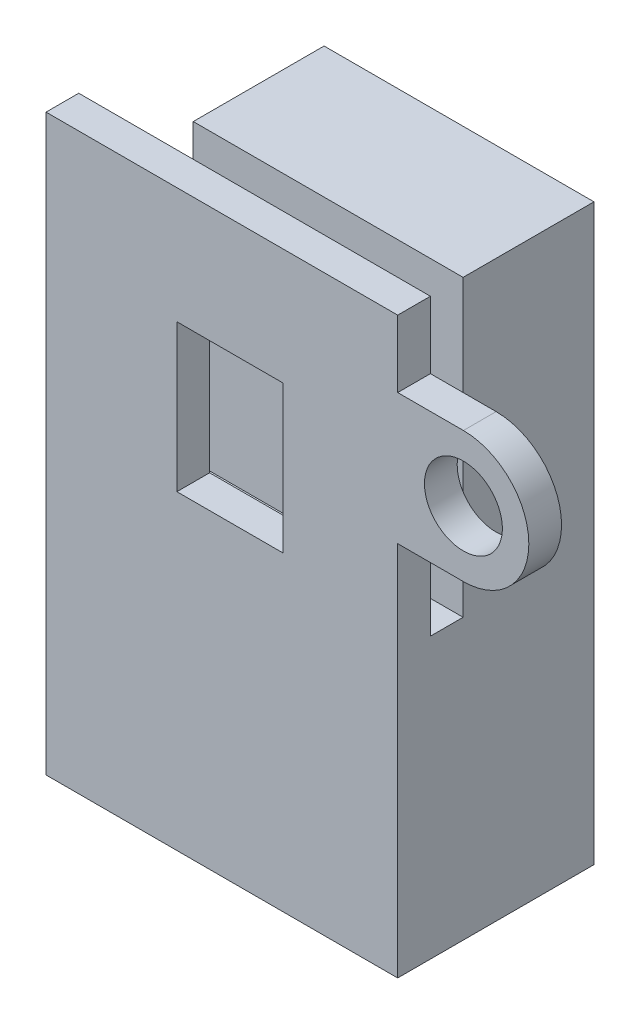
SolidWorks part; units mm, degrees
ref_plane "Front Plane" through (0, 0, 0) normal (0, 0, 1) x (1, 0, 0)
ref_plane "Top Plane" through (0, 0, 0) normal (0, 1, 0) x (1, 0, 0)
ref_plane "Right Plane" through (0, 0, 0) normal (1, 0, 0) x (0, 0, -1)
sketch "Sketch1" plane through (0, 0, 0) normal (1, 0, 0) x (0, 0, -1)
  line L0 (0, 0) -> (0, 37.1)
  line L1 (0, 37.1) -> (-10.6066, 47.7066)
  line L2 (0, 0) -> (12, 0)
  line L3 (12, 0) -> (12, 47.7066)
  line L4 (12, 47.7066) -> (-10.6066, 47.7066)
extrude "Boss-Extrude4" add sketch "Sketch1" along normal blind 16.5
sketch "Sketch4" plane through (0, 0, 0) normal (-1, 0, 0) x (0, 0, 1)
  line L0 (0, 37.1) -> (0, 47.7066)
  line L1 (-12, 47.7066) -> (10.6066, 47.7066) construction
  line L2 (0, 47.7066) -> (10.6066, 47.7066)
  line L3 (10.6066, 47.7066) -> (0, 37.1)
extrude "Cut-Extrude2" cut sketch "Sketch4" against normal blind 1.5
sketch "Sketch5" plane through (16.5, 0, 0) normal (1, 0, 0) x (0, 0, -1)
  line L0 (0, 37.1) -> (-3.567, 40.667)
  line L1 (-10.6066, 47.7066) -> (0, 37.1) construction
  line L2 (-3.567, 40.667) -> (-4.0973, 41.1973)
  line L3 (-4.0973, 41.1973) -> (-3.0366, 42.2579)
  line L4 (-3.0366, 42.2579) -> (-4.4508, 43.6722)
  line L5 (-4.4508, 43.6722) -> (-2.6831, 45.4399)
  line L6 (-3.567, 40.667) -> (-2.8598, 39.9598)
  line L7 (-2.8598, 39.9598) -> (-1.7992, 41.0205)
  line L12 (-2.6831, 45.4399) -> (0, 42.7569)
  line L13 (-1.7992, 41.0205) -> (0, 39.2213)
  line L14 (0, 39.2213) -> (0, 42.7569)
  line M14 (-10.6066, 47.7066) -> (0, 37.1)
extrude "Cut-Extrude4" cut sketch "Sketch5" against normal through all contours L13 L14 L12 L5 L4 L3 L7 M14
sketch "Sketch6" plane through (16.5, 0, 0) normal (1, 0, 0) x (0, 0, -1)
  line L0 (12, 0) -> (12, 2)
  line L1 (12, 0) -> (12, 47.7066) construction
  line L2 (12, 2) -> (0, 2)
  line L3 (0, 37.1) -> (0, 0) construction
  line L4 (0, 2) -> (0, 0)
  line L5 (0, 0) -> (12, 0)
extrude "Cut-Extrude5" cut sketch "Sketch6" against normal through all
sketch "Sketch9" plane through (0, 0, 0) normal (0, 0, 1) x (1, 0, 0)
  line L0 (16.5, 2) -> (16.5, 29)
  line L1 (16.5, 37.1) -> (16.5, 2) construction
  line L2 (16.5, 29) -> (20.5182, 29)
  line L3 (20.5182, 33) -> (16.5, 33)
  line L4 (16.5, 33) -> (16.5, 25)
  line L5 (16.5, 25) -> (20.5182, 25)
  arc A0 (20.5182, 33) -> (20.5182, 25) centre (20.5182, 29) cw
extrude "Boss-Extrude5" add sketch "Sketch9" against normal blind 2
sketch "Sketch10" plane through (0, 0, -2) normal (0, 0, -1) x (-1, 0, 0)
  line L0 (-20.5182, 33) -> (-20.5182, 29)
  circle A0 centre (-20.5182, 29) radius 2.3813
extrude "Cut-Extrude6" cut sketch "Sketch10" against normal through all
sketch "Sketch11" plane through (16.5, 0, 0) normal (1, 0, 0) x (0, 0, -1)
  line L0 (0, 37.1) -> (-10.6066, 47.7066)
  line L1 (-10.6066, 47.7066) -> (12, 47.7066)
  line L2 (0, 37.1) -> (12, 37.1)
  line L3 (12, 2) -> (12, 47.7066) construction
  line L4 (12, 37.1) -> (12, 47.7066)
extrude "Cut-Extrude7" cut sketch "Sketch11" against normal through all
sketch "Sketch12" plane through (0, 2, 0) normal (0, -1, 0) x (1, 0, 0)
  line L0 (16.5, 0) -> (16.5, -6)
  line L1 (16.5, -12) -> (16.5, 0) construction
  line L2 (16.5, -6) -> (8.25, -6)
  circle A0 centre (8.25, -6) radius 2.3813
extrude "Cut-Extrude8" cut sketch "Sketch12" against normal blind 6.35
sketch "Sketch13" plane through (0, 0, 0) normal (0, 0, 1) x (1, 0, 0)
  line L0 (16.5, 2) -> (9.5, 2)
  line L1 (0, 2) -> (16.5, 2) construction
  line L2 (9.5, 2) -> (9.5, 21)
  line L3 (9.5, 21) -> (3, 21)
  line L4 (3, 21) -> (3, 30)
  line L5 (3, 30) -> (9.5, 30)
  line L6 (9.5, 30) -> (9.5, 21)
extrude "Cut-Extrude11" cut sketch "Sketch13" against normal blind 2 contours L3 L4 L5 L6
sketch "Sketch15" plane through (0, 37.1, 0) normal (0, 1, 0) x (1, 0, 0)
  line L0 (0, 0) -> (0, 2)
  line L1 (0, 0) -> (0, 12) construction
  line L2 (0, 2) -> (0, 4)
  line L3 (0, 2) -> (16.5, 2)
  line L4 (16.5, 0) -> (16.5, 12) construction
  line L5 (16.5, 2) -> (16.5, 4)
  line L6 (16.5, 4) -> (0, 4)
  line M3 (16.5, 0) -> (16.5, 12)
  line M5 (0, 12) -> (0, 0)
extrude "Cut-Extrude13" cut sketch "Sketch15" against normal blind 18 contours L6 L3 M3 M5
sketch "Sketch16" plane through (0, 0, 0) normal (-1, 0, 0) x (0, 0, 1)
  line L0 (-2, 37.1) -> (-2, 2)
  line L1 (-12, 2) -> (0, 2) construction
  line L2 (-2, 2) -> (0, 2)
  line L3 (0, 2) -> (0, 37.1)
  line L4 (0, 37.1) -> (-2, 37.1)
extrude "Boss-Extrude6" add sketch "Sketch16" along normal blind 5
